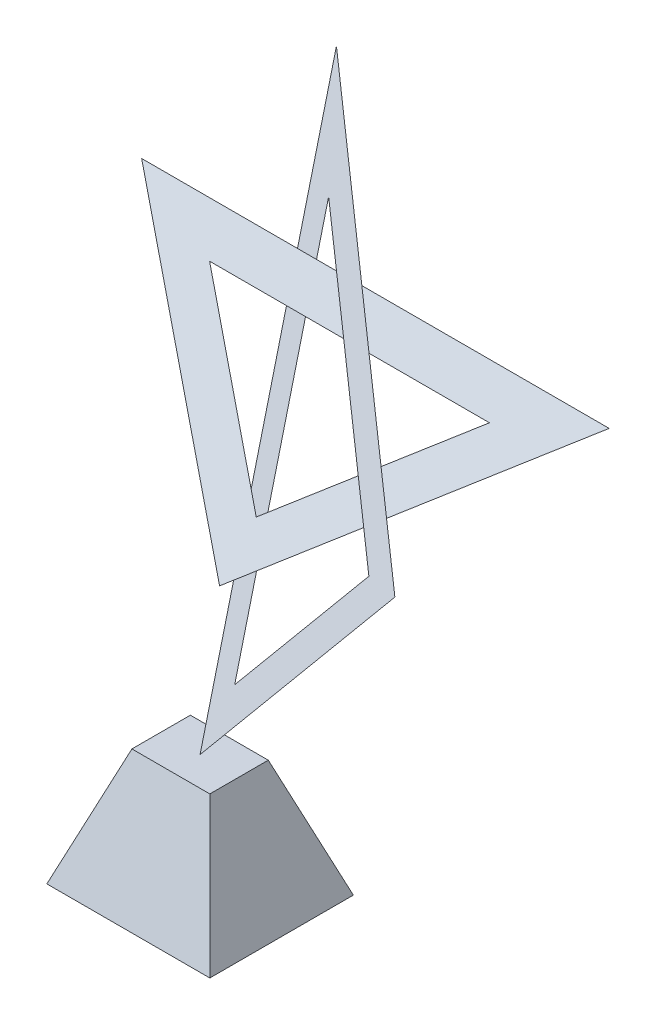
SolidWorks part; units mm, degrees
ref_plane "Front Plane" through (0, 0, 0) normal (0, 0, 1) x (1, 0, 0)
ref_plane "Top Plane" through (0, 0, 0) normal (0, 1, 0) x (1, 0, 0)
ref_plane "Right Plane" through (0, 0, 0) normal (1, 0, 0) x (0, 0, -1)
sketch3d "3DSketch1"
  point P0 (205, 35, 70)
  point P1 (265, 80, 30)
  point P2 (145, 80, 30)
ref_plane "Plane ABC" through (0, 50.2069, 56.4828) normal (0, 0.6644, 0.7474) x (1, 0, 0)
sketch3d "3DSketch2"
  point P0 (205, 0, 75)
  point P1 (250, 55, 70)
  point P2 (170, 105, 5)
ref_plane "Plane DEF" through (9.1667, -9.1667, -18.3333) normal (0.4082, -0.4082, -0.8165) x (-0.9129, -0.1826, -0.3651)
sketch "Sketch3" plane through (0, 50.2069, 56.4828) normal (0, 0.6644, 0.7474) x (1, 0, 0)
  line L0 (265, 39.8618) -> (145, 39.8618)
  line L1 (145, 39.8618) -> (205, -20.3461)
  line L2 (205, -20.3461) -> (265, 39.8618)
  line L3 (240.9168, 29.8618) -> (169.0832, 29.8618)
  line L4 (169.0832, 29.8618) -> (205, -6.1795)
  line L5 (205, -6.1795) -> (240.9168, 29.8618)
  dimension "D1" = 10
surface "Surface-Plane1" sketch "Sketch3"
sketch "Sketch4" plane through (9.1667, -9.1667, -18.3333) normal (0.4082, -0.4082, -0.8165) x (-0.9129, -0.1826, -0.3651)
  line L0 (-263.8197, 17.8885) -> (-214.5247, -33.541)
  line L1 (-214.5247, -33.541) -> (-176.1841, 91.6788)
  line L2 (-176.1841, 91.6788) -> (-263.8197, 17.8885)
  line L3 (-252.1402, 17.2646) -> (-218.1828, -18.1632)
  line L4 (-218.1828, -18.1632) -> (-191.7715, 68.0958)
  line L5 (-191.7715, 68.0958) -> (-252.1402, 17.2646)
  dimension "D1" = 8
surface "Surface-Plane2" sketch "Sketch4"
sketch "Sketch5" plane through (0, 0, 0) normal (0, 1, 0) x (1, 0, 0)
  line L1 (215, -67.5) -> (195, -67.5)
  line L2 (215, -67.5) -> (215, -82.5)
  line L3 (215, -82.5) -> (195, -82.5)
  line L4 (195, -67.5) -> (195, -82.5)
  line L5 (215, -67.5) -> (195, -82.5) construction
  line L6 (215, -82.5) -> (195, -67.5) construction
  point P0 (205, -75)
  dimension "D1" = 15
  dimension "D2" = 20
extrude "Boss-Extrude1" add sketch "Sketch5" against normal blind 30 draft 20
